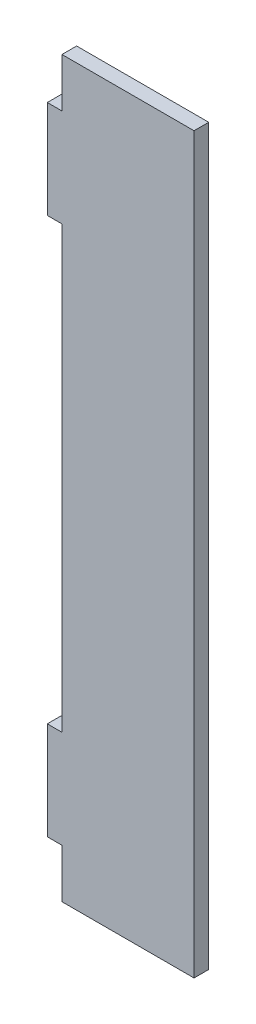
SolidWorks part; units mm, degrees
material "Cedar"
ref_plane "Front Plane" through (0, 0, 0) normal (0, 0, 1) x (1, 0, 0)
ref_plane "Top Plane" through (0, 0, 0) normal (0, 1, 0) x (1, 0, 0)
ref_plane "Right Plane" through (0, 0, 0) normal (1, 0, 0) x (0, 0, -1)
sketch "Sketch1" plane through (0, 0, 0) normal (0, 0, 1) x (1, 0, 0)
  line L1 (-15, -75) -> (15, -75)
  line L2 (-15, -75) -> (-15, 75)
  line L3 (-15, 75) -> (15, 75)
  line L4 (15, -75) -> (15, 75)
  line L5 (-15, -75) -> (15, 75) construction
  line L6 (-15, 75) -> (15, -75) construction
  point P0 (0, 0)
  point P6 (-15, 0)
  dimension "D1" = 30
  dimension "D2" = 75
extrude "Boss-Extrude1" add sketch "Sketch1" along normal blind 3
sketch "Sketch2" plane through (0, 0, 3) normal (0, 0, 1) x (1, 0, 0)
  line L0 (-15, 75) -> (-15, -75) construction
  line L1 (-15, 75) -> (-12, 75)
  line L2 (-15, 75) -> (-15, 65)
  line L3 (-15, 65) -> (-12, 65)
  line L4 (-12, 75) -> (-12, 65)
  line L5 (-15, -75) -> (-12, -75)
  line L6 (-15, -75) -> (-15, -65)
  line L7 (-15, -65) -> (-12, -65)
  line L8 (-12, -75) -> (-12, -65)
  line L9 (-15, 45) -> (-12, 45)
  line L10 (-15, 45) -> (-15, -45)
  line L11 (-15, -45) -> (-12, -45)
  line L12 (-12, 45) -> (-12, -45)
  dimension "D1" = 3
  dimension "D2" = 10
  dimension "D3" = 10
  dimension "D4" = 20
  dimension "D5" = 90
extrude "Cut-Extrude1" cut sketch "Sketch2" against normal blind 3
